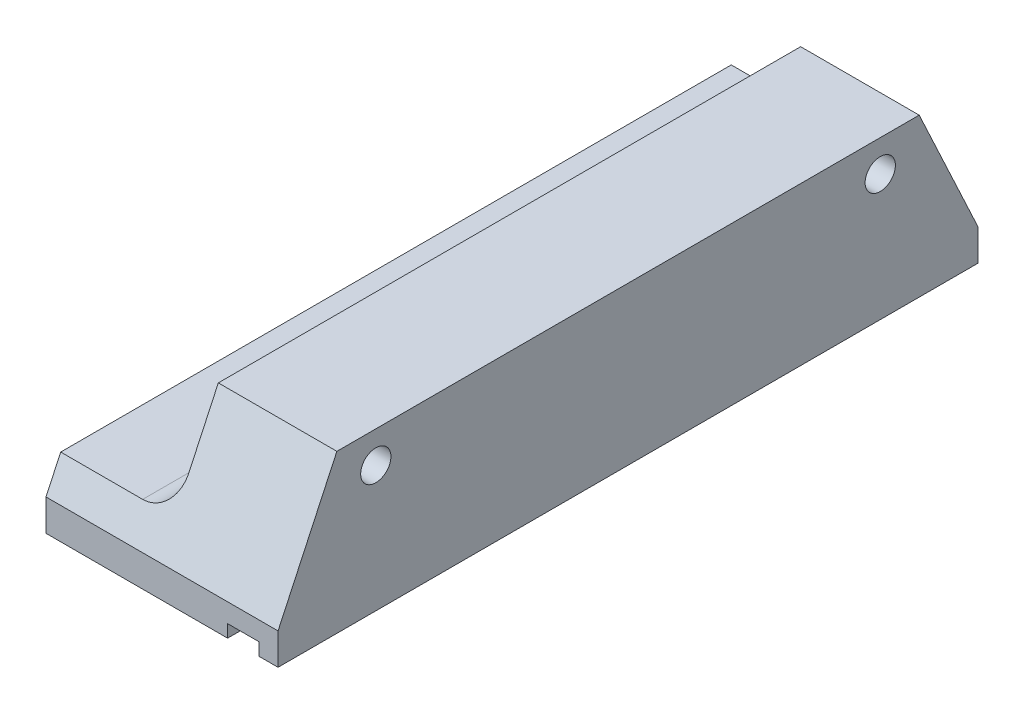
SolidWorks part; units mm, degrees
material "Polyetheretherketone (PEEK)"
ref_plane "Front" through (0, 0, 0) normal (0, 0, 1) x (1, 0, 0)
ref_plane "Top" through (0, 0, 0) normal (0, 1, 0) x (1, 0, 0)
ref_plane "Right" through (0, 0, 0) normal (1, 0, 0) x (0, 0, -1)
sketch "Sketch1" plane through (0, 0, 0) normal (0, 0, 1) x (1, 0, 0)
  line L1 (0, 0) -> (-18.4, 0)
  line L2 (0, 0) -> (0, 12.5)
  line L3 (0, 12.5) -> (-18.4, 12.5)
  line L4 (-18.4, 0) -> (-18.4, 12.5)
  dimension "D1" = 18.4
  dimension "D2" = 12.5
extrude "Boss-Extrude1" add sketch "Sketch1" along normal blind 55.5
sketch "Sketch2" plane through (0, 0, 55.5) normal (0, 0, 1) x (1, 0, 0)
  line L0 (-18.4, 0) -> (0, 0) construction
  line L1 (-1.5, 0) -> (-4, 0)
  line L2 (-1.5, 0) -> (-1.5, 1)
  line L3 (-1.5, 1) -> (-4, 1)
  line L4 (-4, 0) -> (-4, 1)
  line L5 (0, 0) -> (0, 12.5) construction
  dimension "D1" = 1
  dimension "D2" = 2.5
  dimension "D3" = 1.5
extrude "Cut-Extrude1" cut sketch "Sketch2" against normal through all
hole_wizard "M2x0.4 Tapped Hole1" positions "Sketch4" profile "Sketch3" tap size "M2x0.4" standard "ANSI Metric"
sketch "Sketch4" plane through (-18.4, 0, 0) normal (-1, 0, 0) x (0, 0, 1)
  line L0 (55.5, 12.5) -> (0, 12.5) construction
  line L1 (0, 12.5) -> (0, 0) construction
  line L2 (0, 3) -> (3.75, 3) construction
  line L7 (51.75, 3) -> (55.5, 3) construction
  line L8 (55.5, 12.5) -> (55.5, 0) construction
  line L9 (27.75, 3) -> (27.75, 12.5) construction
  line L10 (55.5, 0) -> (0, 0) construction
  point P0 (51.75, 3)
  point P4 (27.75, 3)
  point P8 (3.75, 3)
  dimension "D1" = 3
  dimension "D2" = 24
sketch "Sketch3" plane through (-18.4, 3, 51.75) normal (0, 1, 0) x (0, 0, 1)
  line L0 (0, 0) -> (0, 6.9807)
  line L1 (0, 6.9807) -> (0.8, 6.5)
  line L2 (0.8, 6.5) -> (0.8, 4.5)
  line L3 (0.8, 4.5) -> (1, 4.5)
  line L4 (1, 4.5) -> (1, 0)
  line L5 (1, 0) -> (0, 0)
  line L10 (0, 6.9807) -> (-0.8, 6.5) construction
  line L11 (0, -6.35) -> (0, 107.95) construction
  dimension "Tap Drill Dia." = 1.6
  dimension "Tap Drill Depth" = 6.5
  dimension "Thread Major Dia." = 2
  dimension "Thread Depth" = 4.5
  dimension "Drill Angle" = 118
hole_wizard "CBORE for M2 SHCS1" positions "Sketch6" profile "Sketch5" counterbore size "M2" standard "ANSI Metric" end condition through all
sketch "Sketch6" plane through (-18.4, 0, 0) normal (-1, 0, 0) x (0, 0, 1)
  line L0 (47.75, 10) -> (7.75, 10) construction
  line L1 (7.75, 10) -> (27.75, 10) construction
  line L2 (27.75, 10) -> (27.75, 12.5) construction
  line L3 (55.5, 12.5) -> (0, 12.5) construction
  line L4 (55.5, 0) -> (0, 0) construction
  point P0 (47.75, 10)
  point P4 (7.75, 10)
  dimension "D1" = 40
  dimension "D2" = 10
sketch "Sketch5" plane through (-18.4, 10, 47.75) normal (0, 1, 0) x (0, 0, 1)
  line L0 (0, 0) -> (0, 18.4)
  line L1 (0, 18.4) -> (1.2, 18.4)
  line L3 (1.2, 18.4) -> (1.2, 10.9)
  line L4 (1.2, 10.9) -> (2.2, 10.9)
  line L5 (2.2, 10.9) -> (2.2, 0)
  line L7 (2.2, 0) -> (0, 0)
  line L11 (0, -6.35) -> (0, 107.95) construction
  dimension "Thru Hole Dia." = 2.4
  dimension "Thru Hole Depth" = 18.4
  dimension "C'Bore Dia." = 4.4
  dimension "C'Bore Depth" = 10.9
chamfer "Chamfer1" distance 10 angle 25 1 edges at (-9.2, 12.5, 0)
chamfer "Chamfer2" distance 10 angle 25 1 edges at (-9.2, 12.5, 55.5)
fillet "Fillet1" [suppressed] radius 6
sketch "Sketch7" plane through (-18.4, 0, 0) normal (-1, 0, 0) x (0, 0, 1)
  line L0 (55.5, 0) -> (0, 0) construction
  line L1 (0, 12.5) -> (55.5, 12.5)
  line L2 (0, 12.5) -> (0, 5)
  line L3 (0, 5) -> (55.5, 5)
  line L4 (55.5, 12.5) -> (55.5, 5)
  line L5 (50.8369, 12.5) -> (4.6631, 12.5) construction
  line L6 (0, 2.5) -> (0, 0) construction
  line L7 (55.5, 2.5) -> (55.5, 0) construction
  dimension "D1" = 5
extrude "Cut-Extrude2" cut sketch "Sketch7" against normal blind 9
fillet "Fillet2" radius 2.5 1 edges at (-9.4, 5, 27.75)
